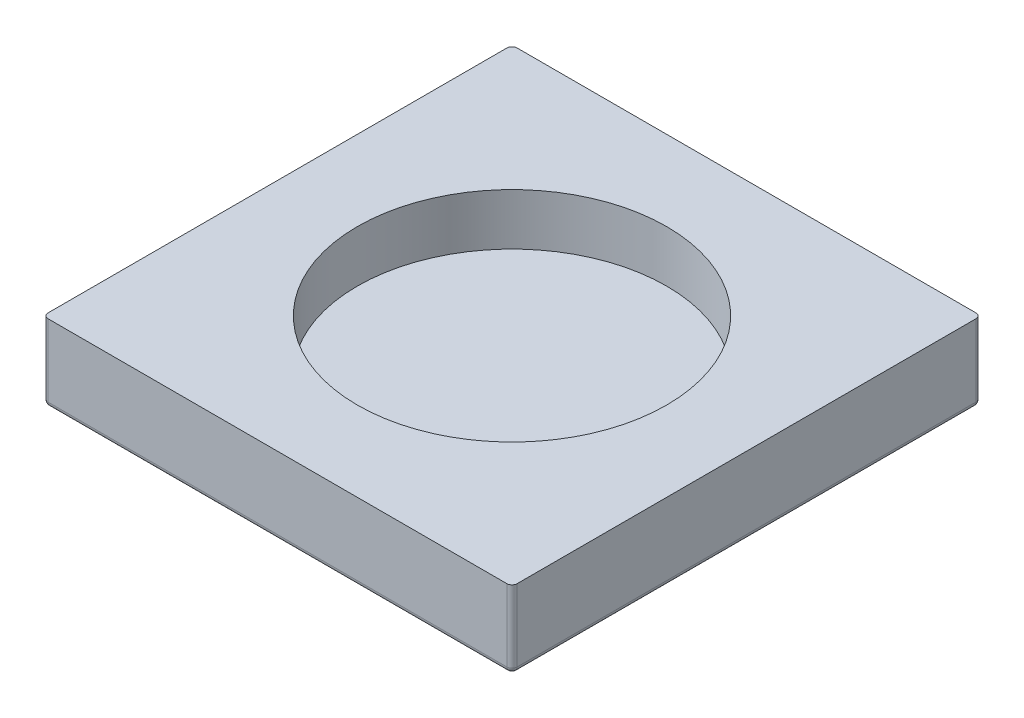
SolidWorks part; units mm, degrees
ref_plane "Front Plane" through (0, 0, 0) normal (0, 0, 1) x (1, 0, 0)
ref_plane "Top Plane" through (0, 0, 0) normal (0, 1, 0) x (1, 0, 0)
ref_plane "Right Plane" through (0, 0, 0) normal (1, 0, 0) x (0, 0, -1)
sketch "Sketch1" plane through (0, 0, 0) normal (0, 1, 0) x (1, 0, 0)
  line L1 (-22.75, -22.75) -> (22.75, -22.75)
  line L2 (-22.75, -22.75) -> (-22.75, 22.75)
  line L3 (-22.75, 22.75) -> (22.75, 22.75)
  line L4 (22.75, -22.75) -> (22.75, 22.75)
  line L5 (-22.75, -22.75) -> (22.75, 22.75) construction
  line L6 (-22.75, 22.75) -> (22.75, -22.75) construction
  point P0 (0, 0)
extrude "Boss-Extrude1" add sketch "Sketch1" along normal blind 7.5
fillet "Fillet1" radius 0.5 8 edges at (22.75, 3.75, 22.75) (-22.75, 3.75, -22.75) (22.75, 3.75, -22.75) (-22.75, 0, 0) (0, 0, -22.75) (22.75, 0, 0) (0, 0, 22.75) (-22.75, 3.75, 22.75)
sketch "Sketch2" plane through (0, 7.5, 0) normal (0, 1, 0) x (1, 0, 0)
  circle A0 centre (0, 0) radius 15
extrude "Cut-Extrude1" cut sketch "Sketch2" against normal blind 5
